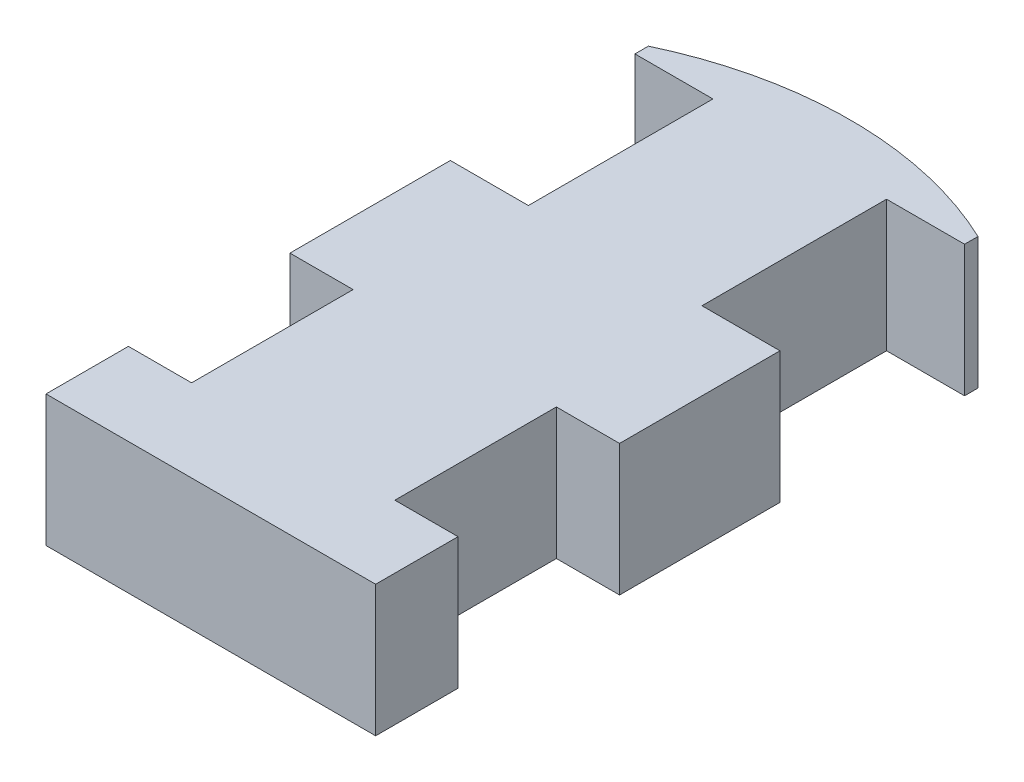
SolidWorks part; units mm, degrees
ref_plane "Front Plane" through (0, 0, 0) normal (0, 0, 1) x (1, 0, 0)
ref_plane "Top Plane" through (0, 0, 0) normal (0, 1, 0) x (1, 0, 0)
ref_plane "Right Plane" through (0, 0, 0) normal (1, 0, 0) x (0, 0, -1)
sketch "Sketch1" plane through (0, 0, 0) normal (0, 1, 0) x (1, 0, 0)
  line L0 (-76.2, 130.6717) -> (0, -29.972) construction
  line L1 (76.2, 147.828) -> (-76.2, 147.828) construction
  line L2 (76.2, 147.828) -> (76.2, -147.828) construction
  line L3 (76.2, -147.828) -> (-76.2, -147.828) construction
  line L4 (-76.2, 147.828) -> (-76.2, -147.828) construction
  line L5 (76.2, 147.828) -> (-76.2, -147.828) construction
  line L6 (76.2, -147.828) -> (-76.2, 147.828) construction
  line L7 (0, -29.972) -> (76.2, 130.6717) construction
  line L8 (-76.2, -109.728) -> (-46.99, -109.728) construction
  line L9 (-76.2, -109.728) -> (-76.2, -35.052) construction
  line L10 (-46.99, -109.728) -> (-46.99, -35.052) construction
  line L11 (-76.2, -35.052) -> (-46.99, -35.052) construction
  line L12 (76.2, -109.728) -> (46.99, -109.728) construction
  line L13 (76.2, -109.728) -> (76.2, -35.052) construction
  line L14 (46.99, -109.728) -> (46.99, -35.052) construction
  line L15 (76.2, -35.052) -> (46.99, -35.052) construction
  line L16 (-76.2, 124.46) -> (-76.2, 39.116) construction
  line L17 (-76.2, 124.46) -> (-40.132, 124.46) construction
  line L18 (-76.2, 39.116) -> (-40.132, 39.116) construction
  line L19 (-40.132, 124.46) -> (-40.132, 39.116) construction
  line L20 (76.2, 124.46) -> (76.2, 39.116) construction
  line L21 (76.2, 124.46) -> (40.132, 124.46) construction
  line L22 (76.2, 39.116) -> (40.132, 39.116) construction
  line L23 (40.132, 124.46) -> (40.132, 39.116) construction
  arc A0 (0, 147.828) -> (76.2, 130.6717) centre (0, -29.972) cw construction
  arc A1 (0, 147.828) -> (-76.2, 130.6717) centre (0, -29.972) ccw construction
  point P0 (0, 0)
  point P6 (0, -147.828)
  point P7 (0, 147.828)
  point P8 (76.2, 124.46)
  point P9 (-76.2, 124.46)
  point P10 (-76.2, -109.728)
  point P11 (76.2, -109.728)
  point P13 (0, -29.972)
  point P17 (76.2, -35.052)
  point P18 (-76.2, -35.052)
  point P19 (-76.2, 39.116)
  point P20 (76.2, 39.116)
  dimension "D1" = 295.656
  dimension "D2" = 152.4
  dimension "D3" = 177.8
  dimension "D4" = 50.754
  dimension "D5" = 74.676
  dimension "D6" = 85.344
  dimension "D7" = 38.1
  dimension "D8" = 74.168
  dimension "D9" = 154.432
  dimension "D10" = 29.21
  dimension "D11" = 29.21
  dimension "D12" = 36.068
  dimension "D13" = 36.068
sketch "Sketch2" plane through (0, 0, 0) normal (0, 1, 0) x (1, 0, 0)
  line L0 (-76.2, -147.828) -> (76.2, -147.828)
  line L1 (76.2, -147.828) -> (76.2, -109.728)
  line L2 (76.2, -109.728) -> (46.99, -109.728)
  line L3 (46.99, -109.728) -> (46.99, -35.052)
  line L4 (46.99, -35.052) -> (76.2, -35.052)
  line L5 (76.2, -35.052) -> (76.2, 39.116)
  line L6 (76.2, 39.116) -> (40.132, 39.116)
  line L7 (40.132, 39.116) -> (40.132, 124.46)
  line L8 (40.132, 124.46) -> (76.2, 124.46)
  line L9 (76.2, 124.46) -> (76.2, 130.6717)
  line L10 (-76.2, 130.6717) -> (-76.2, 124.46)
  line L11 (-76.2, 124.46) -> (-40.132, 124.46)
  line L12 (-40.132, 124.46) -> (-40.132, 39.116)
  line L13 (-40.132, 39.116) -> (-76.2, 39.116)
  line L14 (-76.2, 39.116) -> (-76.2, -35.052)
  line L15 (-76.2, -35.052) -> (-46.99, -35.052)
  line L16 (-46.99, -35.052) -> (-46.99, -109.728)
  line L17 (-46.99, -109.728) -> (-76.2, -109.728)
  line L18 (-76.2, -109.728) -> (-76.2, -147.828)
  arc A0 (-76.2, 130.6717) -> (76.2, 130.6717) centre (0, -29.972) cw
  point P43 (0, 0)
extrude "Boss-Extrude1" add sketch "Sketch2" along normal blind 60.706
sketch "Sketch3" plane through (76.2, 0, 0) normal (1, 0, 0) x (0, 0, -1)
  line L0 (39.116, 60.706) -> (124.46, 60.706) construction
  line L1 (81.788, 0) -> (81.788, 60.706) construction
  line L2 (39.116, 0) -> (124.46, 0) construction
  line L3 (-35.052, 0) -> (-109.728, 0) construction
  line L4 (95.25, 0) -> (95.25, 39.116) construction
  line L5 (95.25, 0) -> (68.58, 0) construction
  line L6 (39.116, 60.706) -> (39.116, 0) construction
  line L7 (124.46, 60.706) -> (124.46, 0) construction
  line L8 (-109.728, 60.706) -> (-35.052, 60.706) construction
  line L9 (-72.39, 0) -> (-72.39, 60.706) construction
  line L10 (95.25, 39.116) -> (68.58, 39.116) construction
  line L11 (68.58, 0) -> (68.58, 39.116) construction
  line L12 (34.544, 0) -> (34.544, 60.706) construction
  line L13 (34.544, 0) -> (14.478, 0) construction
  line L14 (34.544, 60.706) -> (14.478, 60.706) construction
  line L15 (14.478, 0) -> (14.478, 60.706) construction
  line L16 (-35.052, 60.706) -> (39.116, 60.706) construction
  line L17 (-147.828, 0) -> (-109.728, 0) construction
  line L18 (-141.732, 0) -> (-141.732, 29.21) construction
  line L19 (-141.732, 0) -> (-88.392, 0) construction
  line L20 (-141.732, 29.21) -> (-88.392, 29.21) construction
  line L21 (-88.392, 0) -> (-88.392, 29.21) construction
  line L22 (-93.98, 0) -> (-93.98, 40.894) construction
  line L23 (-93.98, 0) -> (-59.436, 0) construction
  line L24 (-93.98, 40.894) -> (-59.436, 40.894) construction
  line L25 (-59.436, 0) -> (-59.436, 40.894) construction
  line L26 (-57.658, 0) -> (-57.658, 57.15) construction
  line L27 (-57.658, 0) -> (-13.208, 0) construction
  line L28 (-57.658, 57.15) -> (-13.208, 57.15) construction
  line L29 (-13.208, 0) -> (-13.208, 57.15) construction
  line L30 (-147.828, 0) -> (-147.828, 6.35) construction
  line L31 (-147.828, 0) -> (175.26, 0) construction
  line L32 (-147.828, 6.35) -> (175.26, 6.35) construction
  line L33 (175.26, 0) -> (175.26, 6.35) construction
  line L34 (-147.828, 60.706) -> (-147.828, 0) construction
  point P9 (81.788, 60.706)
  point P14 (81.788, 60.706)
  point P18 (-72.39, 60.706)
  point P21 (-72.39, 60.706)
  point P24 (-72.39, 23.368)
  point P25 (81.788, 23.368)
  point P26 (-72.39, 68.453)
  point P27 (81.788, 68.453)
  point P28 (34.544, 0)
  point P31 (95.25, 0)
  point P40 (-141.732, 0)
  point P62 (-141.732, 6.35)
  point P63 (-141.732, 6.35)
  point P64 (95.25, 6.35)
  point P65 (95.25, 6.35)
  point P66 (-93.98, 29.21)
  point P67 (-93.98, 29.21)
  dimension "D1" = 42.672
  dimension "D2" = 42.672
  dimension "D3" = 23.368
  dimension "D4" = 45.085
  dimension "D5" = 154.178
  dimension "D6" = 29.21
  dimension "D7" = 26.67
  dimension "D8" = 39.116
  dimension "D9" = 34.036
  dimension "D10" = 60.706
  dimension "D11" = 20.066
  dimension "D12" = 6.096
  dimension "D13" = 29.21
  dimension "D14" = 53.34
  dimension "D15" = 40.894
  dimension "D16" = 5.588
  dimension "D17" = 34.544
  dimension "D18" = 1.778
  dimension "D19" = 44.45
  dimension "D20" = 6.35
  dimension "D21" = 50.8
  dimension "D22" = 50.8
sketch "Sketch5" plane through (76.2, 0, 0) normal (1, 0, 0) x (0, 0, -1)
  line L0 (-147.828, 6.35) -> (-141.732, 6.35)
  line L1 (-141.732, 6.35) -> (-141.732, 29.21)
  line L2 (-141.732, 29.21) -> (-93.98, 29.21)
  line L3 (-93.98, 29.21) -> (-93.98, 40.894)
  line L4 (-93.98, 40.894) -> (-59.436, 40.894)
  line L5 (-59.436, 40.894) -> (-57.658, 57.15)
  line L6 (-57.658, 57.15) -> (-13.208, 57.15)
  line L7 (-13.208, 57.15) -> (14.478, 60.706)
  line L8 (14.478, 60.706) -> (34.544, 60.706)
  line L9 (34.544, 60.706) -> (68.58, 39.116)
  line L10 (68.58, 39.116) -> (95.25, 39.116)
  line L11 (95.25, 39.116) -> (95.25, 6.35)
  line L12 (95.25, 6.35) -> (175.26, 6.35)
  line L13 (175.26, 6.35) -> (175.26, 113.9715)
  line L14 (175.26, 113.9715) -> (-147.828, 113.9715)
  line L15 (-147.828, 113.9715) -> (-147.828, 6.35)
sketch "Sketch6" plane through (0, 0, 147.828) normal (0, 0, 1) x (1, 0, 0)
  line L0 (76.2, 78.3506) -> (76.2, 0)
  line L1 (-76.2, 0) -> (-76.2, 107.95) construction
  line L2 (-76.2, 0) -> (76.2, 0) construction
  line L3 (-76.2, 107.95) -> (76.2, 107.95) construction
  line L4 (0, 0) -> (0, 66.4501) construction
  line L5 (76.2, 0) -> (76.2, 107.95) construction
  line L6 (76.2, 0) -> (-76.2, 0)
  line L7 (63.5, 88.9) -> (76.2, 88.9) construction
  line L8 (63.5, 88.9) -> (48.5369, 81.9226) construction
  line L9 (76.2, 0) -> (-76.2, 0)
  line L10 (48.5369, 81.9226) -> (-48.5369, 81.9226) construction
  line L11 (48.5369, 81.9226) -> (33.2969, 81.9226)
  line L12 (-63.5, 88.9) -> (-48.5369, 81.9226) construction
  line L13 (-63.5, 88.9) -> (-76.2, 88.9) construction
  line L14 (-76.2, 0) -> (-76.2, 107.95) construction
  line L15 (-48.5369, 81.9226) -> (-33.2969, 81.9226)
  line L16 (-76.2, 78.3506) -> (-76.2, 0)
  arc A0 (48.5369, 81.9226) -> (80.01, 88.9) centre (63.5, 88.9) cw
  arc A1 (80.01, 88.9) -> (76.2, 78.3506) centre (63.5, 88.9) cw
  circle A2 centre (63.5, 88.9) radius 16.51 construction
  circle A3 centre (-63.5, 88.9) radius 16.51 construction
  arc A4 (-80.01, 88.9) -> (-76.2, 78.3506) centre (-63.5, 88.9) ccw
  arc A5 (-48.5369, 81.9226) -> (-80.01, 88.9) centre (-63.5, 88.9) ccw
  ellipse E0 centre (0, 81.9226) end of major axis (33.2969, 81.9226) minor radius 12.7 (-33.2969, 81.9226) -> (33.2969, 81.9226) cw
  point P10 (76.2, 88.9)
  point P11 (0, 97.0305)
  point P17 (63.5, 107.95)
  point P18 (63.5, 88.9)
  point P19 (0, 96.3471)
  point P26 (0, 107.95)
  point P28 (0, 90.8215)
  point P35 (-63.5, 107.95)
  dimension "D4" = 33.02
  dimension "D1" = 107.95
  dimension "D2" = 19.05
  dimension "D3" = 12.7
  dimension "D5" = 205
  dimension "D6" = 15.24
  dimension "D7" = 12.7
